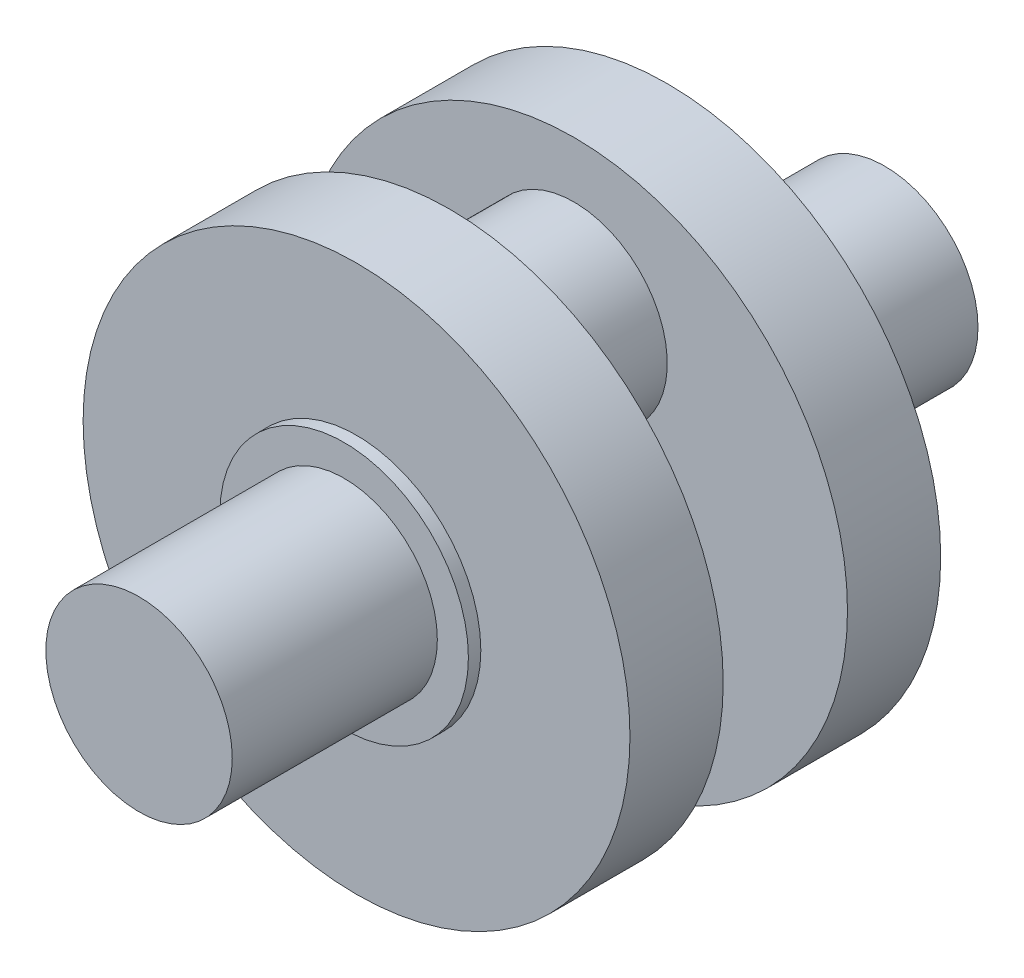
SolidWorks part; units mm, degrees
ref_plane "Płaszczyzna przednia" through (0, 0, 0) normal (0, 0, 1) x (1, 0, 0)
ref_plane "Płaszczyzna górna" through (0, 0, 0) normal (0, 1, 0) x (1, 0, 0)
ref_plane "Płaszczyzna prawa" through (0, 0, 0) normal (1, 0, 0) x (0, 0, -1)
sketch "Szkic1" plane through (0, 0, 0) normal (0, 0, 1) x (1, 0, 0)
  circle A0 centre (0, 0) radius 15
  dimension "D1" = 30
extrude "Dodanie-wyciągnięcie1" add sketch "Szkic1" along normal blind 33
sketch "Szkic2" plane through (0, 0, 0) normal (0, 0, 1) x (1, 0, 0)
  circle A0 centre (0, 0) radius 20
  dimension "D1" = 40
extrude "Dodanie-wyciągnięcie2" add sketch "Szkic2" against normal blind 2
sketch "Szkic3" plane through (0, 0, -2) normal (0, 0, -1) x (-1, 0, 0)
  circle A0 centre (0, 0) radius 44
  dimension "D1" = 88
extrude "Dodanie-wyciągnięcie3" add sketch "Szkic3" along normal blind 15
sketch "Szkic4" plane through (0, 0, -17) normal (0, 0, -1) x (-1, 0, 0)
  circle A0 centre (0, 20) radius 15
  dimension "D1" = 30
  dimension "D2" = 20
extrude "Dodanie-wyciągnięcie4" add sketch "Szkic4" along normal blind 10
mirror "Lustro2" about plane through (0, 20, -27) normal (0, 0, -1) of bodies 104
